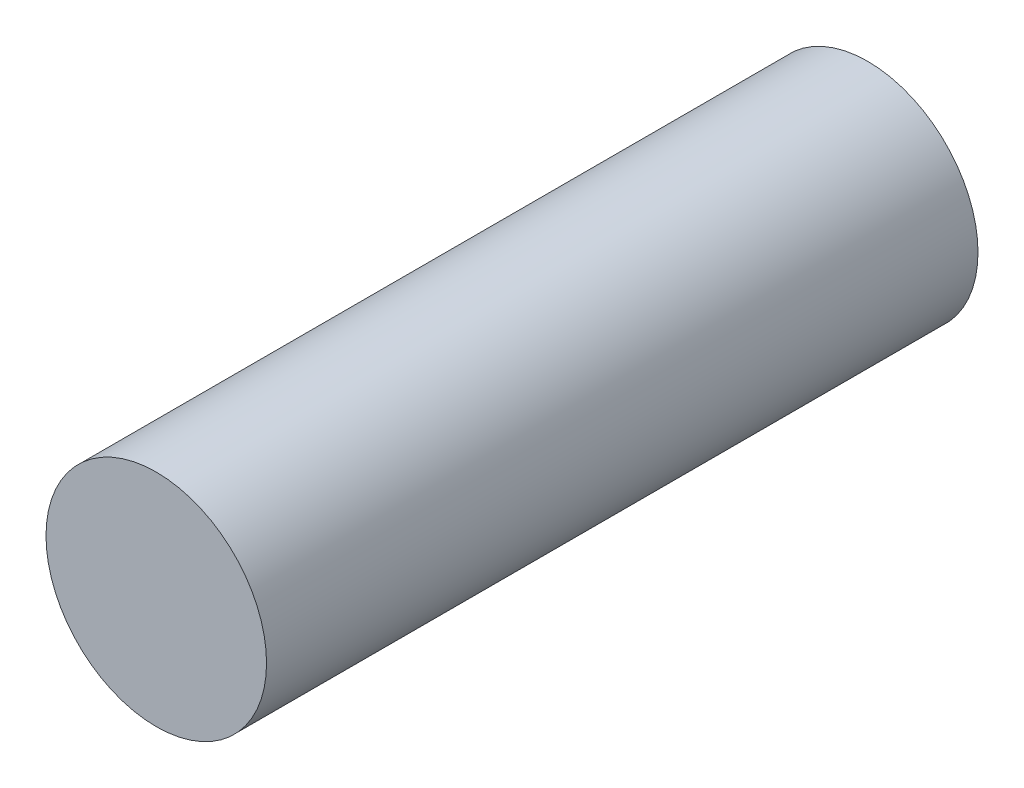
SolidWorks part; units mm, degrees
ref_plane "Front Plane" through (0, 0, 0) normal (0, 0, 1) x (1, 0, 0)
ref_plane "Top Plane" through (0, 0, 0) normal (0, 1, 0) x (1, 0, 0)
ref_plane "Right Plane" through (0, 0, 0) normal (1, 0, 0) x (0, 0, -1)
sketch "Sketch1" plane through (0, 0, 0) normal (0, 0, 1) x (1, 0, 0)
  circle A0 centre (0, 0) radius 7.75
  dimension "D1" = 15.5
extrude "Boss-Extrude1" add sketch "Sketch1" along normal blind 50
